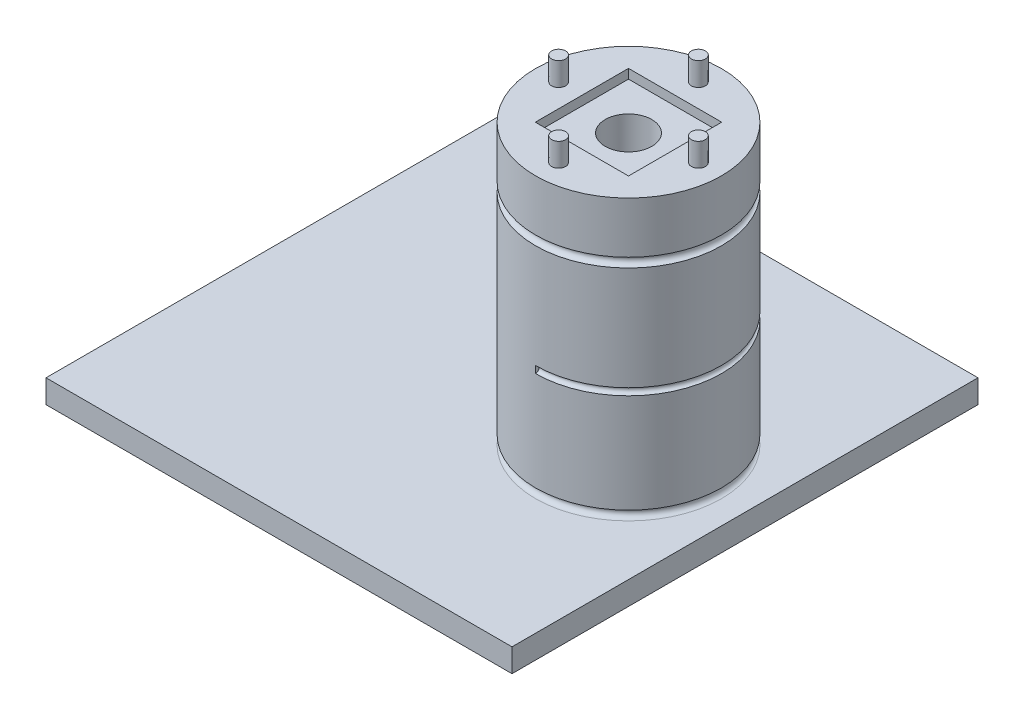
SolidWorks part; units mm, degrees
ref_plane "Front Plane" through (0, 0, 0) normal (0, 0, 1) x (1, 0, 0)
ref_plane "Top Plane" through (0, 0, 0) normal (0, 1, 0) x (1, 0, 0)
ref_plane "Right Plane" through (0, 0, 0) normal (1, 0, 0) x (0, 0, -1)
sketch "Sketch2" plane through (0, 0, 0) normal (0, 1, 0) x (1, 0, 0)
  line L1 (25, 50) -> (-75, 50)
  line L2 (25, 50) -> (25, -50)
  line L3 (25, -50) -> (-75, -50)
  line L4 (-75, 50) -> (-75, -50)
  line L5 (25, 50) -> (-75, -50) construction
  line L6 (25, -50) -> (-75, 50) construction
  point P0 (0, 0)
extrude "Boss-Extrude1" add sketch "Sketch2" along normal blind 5
sketch "Sketch3" plane through (0, 5, 0) normal (0, 1, 0) x (1, 0, 0)
  circle A0 centre (0, 0) radius 19.95
extrude "Boss-Extrude2" add sketch "Sketch3" along normal blind 60
sketch "Sketch4" plane through (0, 65, 0) normal (0, 1, 0) x (1, 0, 0)
  circle A1 centre (0, 0) radius 5
extrude "Cut-Extrude1" cut sketch "Sketch4" against normal blind 43.5 contours A1
sketch "Sketch10" plane through (0, 0, 0) normal (0, 0, 1) x (1, 0, 0)
  line L0 (19.95, 5) -> (19.95, 65) construction
  line L1 (0, 0) -> (0, 69.612) construction
  circle A0 centre (19.95, 6) radius 1
revolve "Cut-Revolve2" cut sketch "Sketch10" angle 360 about L1
sketch "Sketch11" plane through (0, 0, 0) normal (0, 0, 1) x (1, 0, 0)
  line L1 (0, 0) -> (0, 68.8021) construction
  circle A0 centre (19.95, 53) radius 1
revolve "Cut-Revolve3" cut sketch "Sketch11" angle 360 about L1
ref_plane "Plane1" through (0, 38, 0) normal (0, 1, 0) x (1, 0, 0)
sketch "Sketch15" plane through (0, 38, 0) normal (0, 1, 0) x (1, 0, 0)
  circle A0 centre (0, 0) radius 5
  point P3 (0, 0)
extrude "Boss-Extrude3" add sketch "Sketch15" along normal blind 10 and the other way blind 2
sketch "Sketch18" plane through (0, 65, 0) normal (0, 1, 0) x (1, 0, 0)
  circle A0 centre (0, 0) radius 5
extrude "Boss-Extrude4" add sketch "Sketch18" against normal blind 1
sketch "Sketch19" plane through (0, 65, 0) normal (0, 1, 0) x (1, 0, 0)
  circle A0 centre (0, 0) radius 2.7
extrude "Cut-Extrude3" cut sketch "Sketch19" against normal blind 36
sketch "Sketch20" plane through (0, 0, 0) normal (1, 0, 0) x (0, 0, -1)
  line L0 (-19.95, 52) -> (-19.95, 7) construction
  line L1 (0, 0) -> (0, 69.1538) construction
  line L2 (-50, 0) -> (50, 0) construction
  circle A0 centre (-19.95, 29) radius 0.75
revolve "Cut-Revolve4" cut sketch "Sketch20" angle 180 about L1
sketch "Sketch21" plane through (0, 65, 0) normal (0, 1, 0) x (1, 0, 0)
  line L1 (-10, -10) -> (10, -10)
  line L2 (-10, -10) -> (-10, 10)
  line L3 (-10, 10) -> (10, 10)
  line L4 (10, -10) -> (10, 10)
  line L5 (-10, -10) -> (10, 10) construction
  line L6 (-10, 10) -> (10, -10) construction
  point P0 (0, 0)
extrude "Cut-Extrude4" cut sketch "Sketch21" against normal blind 2
sketch "Sketch23" plane through (0, 65, 0) normal (0, 1, 0) x (1, 0, 0)
  circle A0 centre (0, -15) radius 1.5
  circle A1 centre (0, 15) radius 1.5
  circle A2 centre (-15, 0) radius 1.5
  circle A3 centre (15, 0) radius 1.5
extrude "Boss-Extrude5" add sketch "Sketch23" along normal blind 5
